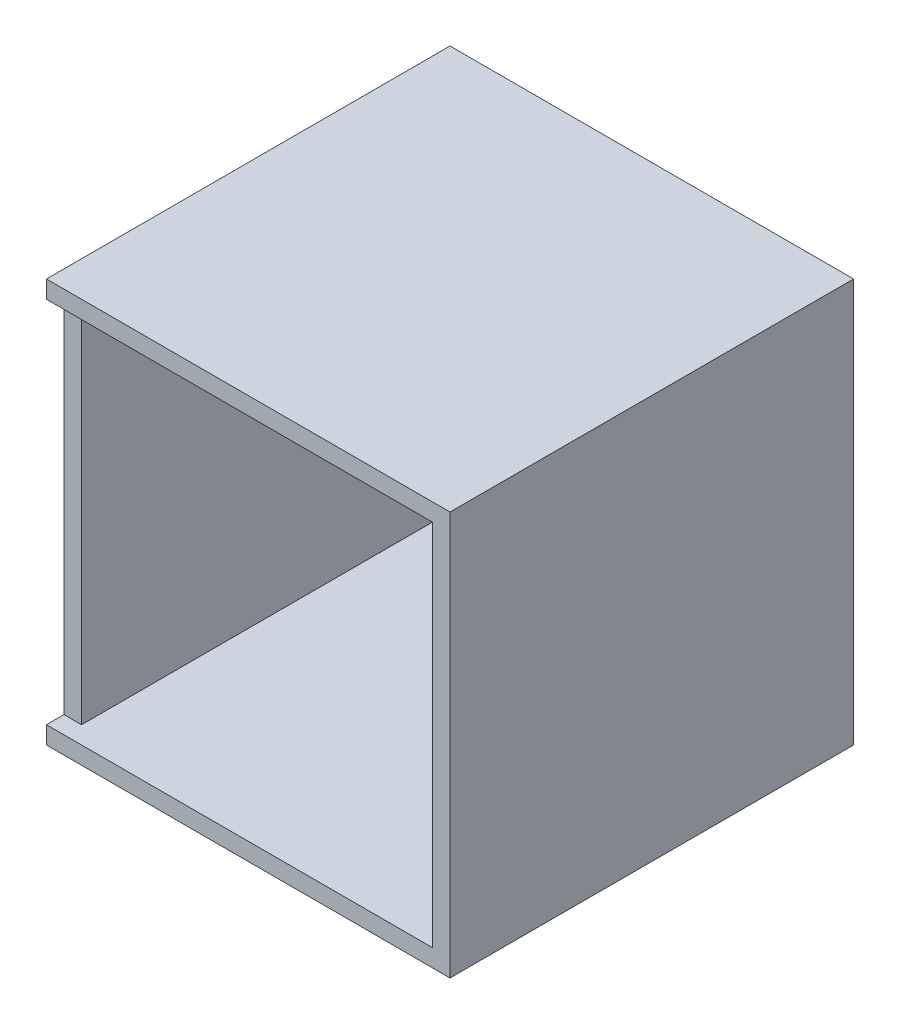
SolidWorks part; units mm, degrees
ref_plane "Front Plane" through (0, 0, 0) normal (0, 0, 1) x (1, 0, 0)
ref_plane "Top Plane" through (0, 0, 0) normal (0, 1, 0) x (1, 0, 0)
ref_plane "Right Plane" through (0, 0, 0) normal (1, 0, 0) x (0, 0, -1)
sketch "Sketch2" plane through (0, 0, 0) normal (0, 0, 1) x (1, 0, 0)
  line L1 (-146.05, 146.05) -> (146.05, 146.05)
  line L2 (-146.05, 146.05) -> (-146.05, -146.05)
  line L3 (-146.05, -146.05) -> (146.05, -146.05)
  line L4 (146.05, 146.05) -> (146.05, -146.05)
  line L5 (-146.05, 146.05) -> (146.05, -146.05) construction
  line L6 (-146.05, -146.05) -> (146.05, 146.05) construction
  point P0 (0, 0)
  dimension "D1" = 292.1
  dimension "D2" = 292.1
extrude "Boss-Extrude1" add sketch "Sketch2" along normal mid plane 292.1
shell "Shell1" thickness 12.7
sketch "Sketch3" plane through (0, 0, 146.05) normal (0, 0, 1) x (1, 0, 0)
  line L0 (-133.35, 133.35) -> (-133.35, -133.35) construction
  line L1 (-111.2893, 133.35) -> (-155.4107, 133.35)
  line L2 (-111.2893, 133.35) -> (-111.2893, -133.35)
  line L3 (-111.2893, -133.35) -> (-155.4107, -133.35)
  line L4 (-155.4107, 133.35) -> (-155.4107, -133.35)
  line L5 (-111.2893, 133.35) -> (-155.4107, -133.35) construction
  line L6 (-111.2893, -133.35) -> (-155.4107, 133.35) construction
  point P0 (-133.35, 0)
  dimension "D1" = 266.7
extrude "Cut-Extrude1" cut sketch "Sketch3" against normal blind 12.7
sketch "Sketch4" plane through (0, 0, -146.05) normal (0, 0, -1) x (-1, 0, 0)
  line L0 (-146.05, -146.05) -> (-146.05, 146.05) construction
  line L1 (-95.25, -84.328) -> (-86.36, -84.328)
  line L2 (-95.25, -84.328) -> (-95.25, -95.25)
  line L3 (-95.25, -95.25) -> (-86.36, -95.25)
  line L4 (-86.36, -84.328) -> (-86.36, -95.25)
  line L5 (-95.25, -84.328) -> (-86.36, -95.25) construction
  line L6 (-95.25, -95.25) -> (-86.36, -84.328) construction
  line L7 (146.05, -146.05) -> (-146.05, -146.05) construction
  point P0 (-90.805, -89.789)
  dimension "D1" = 8.89
  dimension "D2" = 10.922
  dimension "D3" = 50.8
  dimension "D4" = 50.8
extrude "Cut-Extrude2" cut sketch "Sketch4" against normal blind 2.54
